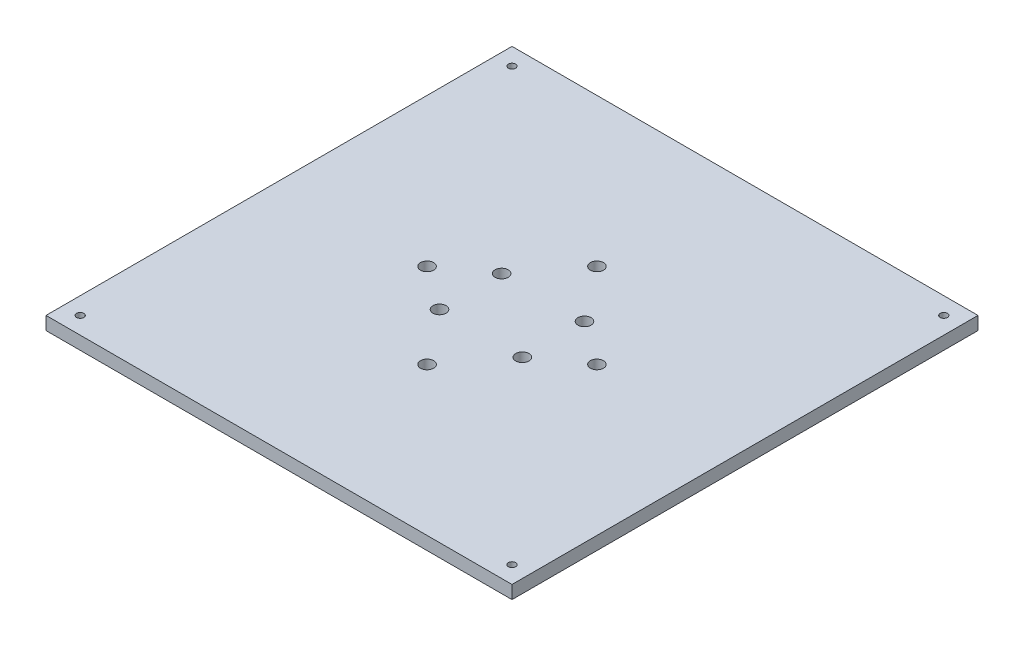
SolidWorks part; units mm, degrees
ref_plane "Front Plane" through (0, 0, 0) normal (0, 0, 1) x (1, 0, 0)
ref_plane "Top Plane" through (0, 0, 0) normal (0, 1, 0) x (1, 0, 0)
ref_plane "Right Plane" through (0, 0, 0) normal (1, 0, 0) x (0, 0, -1)
sketch "Sketch1" plane through (0, 0, 0) normal (0, 1, 0) x (1, 0, 0)
  line L1 (0, 0) -> (225, 0)
  line L2 (0, 0) -> (0, 225)
  line L3 (0, 225) -> (225, 225)
  line L4 (225, 0) -> (225, 225)
  line L5 (0, 0) -> (225, 225) construction
  line L6 (0, 225) -> (225, 0) construction
  point P4 (112.5, 112.5)
  dimension "D1" = 225
  dimension "D2" = 225
extrude "Boss-Extrude1" add sketch "Sketch1" along normal blind 6.35
sketch "Sketch2" plane through (0, 6.35, 0) normal (0, 1, 0) x (1, 0, 0)
  line L0 (222.5, 222.5) -> (222.5, 225) construction
  line L1 (2.5, 2.5) -> (222.5, 2.5) construction
  line L2 (2.5, 2.5) -> (2.5, 222.5) construction
  line L3 (2.5, 222.5) -> (222.5, 222.5) construction
  line L4 (222.5, 2.5) -> (222.5, 222.5) construction
  line L5 (112.5, 222.5) -> (112.5, 2.5) construction
  line L6 (2.5, 112.5) -> (222.5, 112.5) construction
  line L7 (225, 225) -> (0, 225) construction
  line L8 (222.5, 222.5) -> (225, 222.5) construction
  line L9 (225, 0) -> (225, 225) construction
  line L10 (2.5, 2.5) -> (0, 2.5) construction
  line L11 (0, 225) -> (0, 0) construction
  line L12 (2.5, 2.5) -> (2.5, 0) construction
  line L13 (0, 0) -> (225, 0) construction
  circle A0 centre (216.74, 216.74) radius 1.75
  circle A1 centre (8.26, 216.74) radius 1.75
  circle A2 centre (216.74, 8.26) radius 1.75
  circle A3 centre (8.26, 8.26) radius 1.75
  dimension "D2" = 5.76
  dimension "D4" = 3.5
  dimension "D1" = 220
  dimension "D3" = 5.76
extrude "Cut-Extrude1" cut sketch "Sketch2" against normal through all
sketch "Sketch3" plane through (0, 6.35, 0) normal (0, 1, 0) x (1, 0, 0)
  line L0 (112.5, 0) -> (112.5, 71.4904) construction
  line L3 (0, 0) -> (225, 0) construction
  line L6 (225, 112.5) -> (153.5096, 112.5) construction
  line L7 (153.5096, 71.4904) -> (71.4904, 71.4904)
  line L8 (153.5096, 71.4904) -> (153.5096, 153.5096)
  line L9 (153.5096, 153.5096) -> (71.4904, 153.5096)
  line L10 (71.4904, 71.4904) -> (71.4904, 153.5096)
  line L11 (225, 0) -> (225, 225) construction
  line L12 (0, 112.5) -> (71.4904, 112.5) construction
  line L13 (0, 225) -> (0, 0) construction
  line L14 (112.5, 225) -> (112.5, 153.5096) construction
  line L15 (225, 225) -> (0, 225) construction
  line L16 (112.5, 71.4904) -> (112.5, 153.5096) construction
  line L17 (153.5096, 112.5) -> (71.4904, 112.5) construction
  circle A0 centre (112.5, 71.4904) radius 3.175
  circle A1 centre (71.4904, 112.5) radius 3.175
  circle A2 centre (112.5, 153.5096) radius 3.175
  circle A3 centre (153.5096, 112.5) radius 3.175
  circle A4 centre (92.5, 97.5) radius 3.175
  circle A5 centre (92.5, 127.5) radius 3.175
  circle A6 centre (132.5, 127.5) radius 3.175
  circle A7 centre (132.5, 97.5) radius 3.175
  point P20 (112.5, 153.5096)
  point P22 (153.5096, 112.5)
  dimension "D2" = 6.35
  dimension "D1" = 82.0192
  dimension "D3" = 20
  dimension "D4" = 15
  dimension "D5" = 20
  dimension "D6" = 15
extrude "Cut-Extrude2" cut sketch "Sketch3" against normal through all contours L8 A3 | L8 A3 | A6 | A7 | A4 | A5 | L10 A1 | L10 A1 | L9 A2 | L9 A2 | L7 A0 | L7 A0
